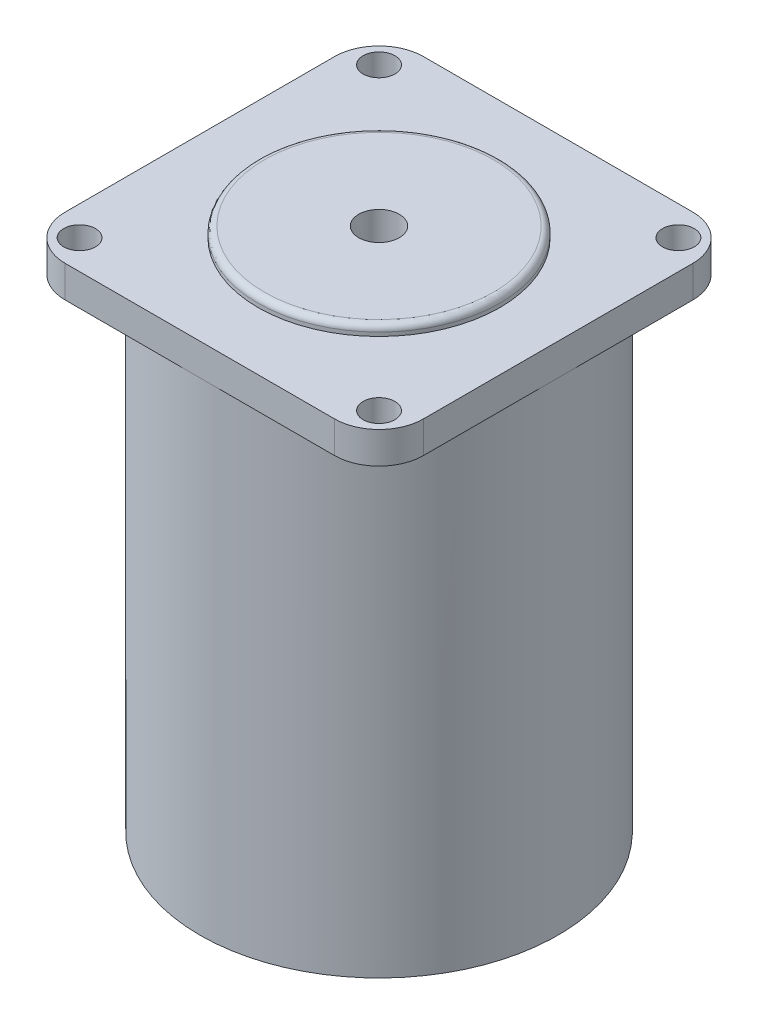
SolidWorks part; units mm, degrees
material "1060 Alloy"
ref_plane "Front" through (0, 0, 0) normal (0, 0, 1) x (1, 0, 0)
ref_plane "Top" through (0, 0, 0) normal (0, 1, 0) x (1, 0, 0)
ref_plane "Right" through (0, 0, 0) normal (1, 0, 0) x (0, 0, -1)
sketch "Sketch1" plane through (0, 0, 0) normal (0, 1, 0) x (1, 0, 0)
  circle A0 centre (0, 0) radius 28.2
extrude "Boss-Extrude1" add sketch "Sketch1" along normal blind 76
sketch "Sketch2" plane through (0, 76, 0) normal (0, 1, 0) x (1, 0, 0)
  line L1 (-21.2, -28.2) -> (21.2, -28.2)
  line L2 (-28.2, -21.2) -> (-28.2, 21.2)
  line L3 (-21.2, 28.2) -> (21.2, 28.2)
  line L4 (28.2, -21.2) -> (28.2, 21.2)
  line L5 (-28.2, -28.2) -> (28.2, 28.2) construction
  line L6 (-28.2, 28.2) -> (28.2, -28.2) construction
  arc A1 (-21.2, 28.2) -> (-28.2, 21.2) centre (-21.2, 21.2) ccw
  arc A2 (28.2, 21.2) -> (21.2, 28.2) centre (21.2, 21.2) ccw
  arc A3 (21.2, -28.2) -> (28.2, -21.2) centre (21.2, -21.2) ccw
  arc A4 (-21.2, -28.2) -> (-28.2, -21.2) centre (-21.2, -21.2) cw
  point P0 (0, 0)
  dimension "D1" = 56.4
  dimension "D3" = 7
  dimension "D4" = 7
  dimension "D5" = 7
  dimension "D6" = 7
  dimension "D2" = 56.4
extrude "Boss-Extrude3" add sketch "Sketch2" along normal blind 5
sketch "Sketch4" plane through (0, 81, 0) normal (0, 1, 0) x (1, 0, 0)
  line L5 (-23.57, 23.57) -> (23.57, -23.57) construction
  line L6 (-23.57, -23.57) -> (23.57, 23.57) construction
  circle A0 centre (-23.57, 23.57) radius 2.5
  circle A1 centre (23.57, 23.57) radius 2.5
  circle A2 centre (-23.57, -23.57) radius 2.5
  circle A3 centre (23.57, -23.57) radius 2.5
  point P0 (0, 0)
  dimension "D3" = 47.14
  dimension "D1" = 47.14
  dimension "D2" = 47.14
  dimension "D4" = 47.14
extrude "Cut-Extrude1" cut sketch "Sketch4" against normal blind 5
sketch "Sketch5" plane through (0, 81, 0) normal (0, 1, 0) x (1, 0, 0)
  circle A0 centre (0, 0) radius 19.05
extrude "Boss-Extrude4" add sketch "Sketch5" along normal blind 1.6 contours A0
fillet "Fillet1" radius 1 1 edges at (0, 82.6, 19.05)
sketch "Sketch7" plane through (0, 82.6, 0) normal (0, 1, 0) x (1, 0, 0)
  circle A0 centre (0, 0) radius 3.2
extrude "Cut-Extrude3" cut sketch "Sketch7" against normal through all
